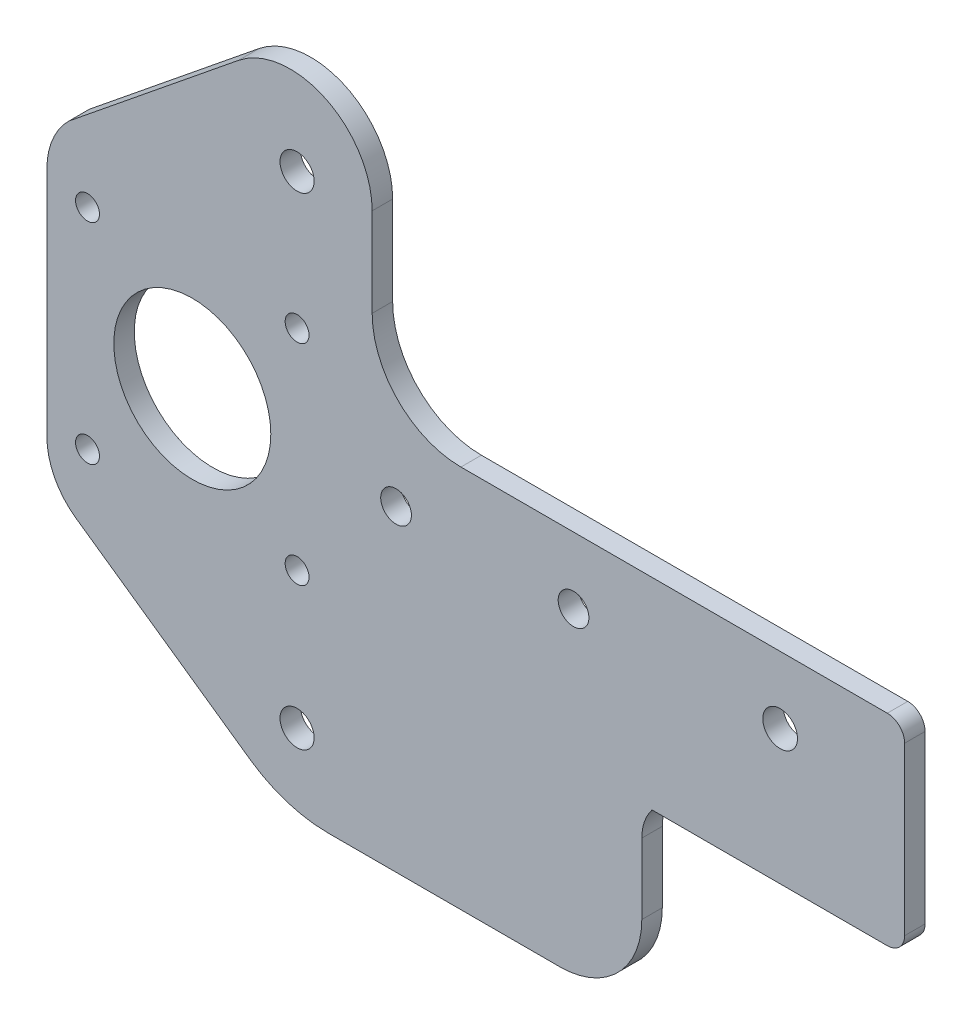
SolidWorks part; units mm, degrees
ref_plane "Front Plane" through (0, 0, 0) normal (0, 0, 1) x (1, 0, 0)
ref_plane "Top Plane" through (0, 0, 0) normal (0, 1, 0) x (1, 0, 0)
ref_plane "Right Plane" through (0, 0, 0) normal (1, 0, 0) x (0, 0, -1)
sketch "Sketch1" plane through (0, 0, 0) normal (0, 0, 1) x (1, 0, 0)
  line L0 (0, 0) -> (0, -29.5)
  line L1 (0, -29.5) -> (-37, -29.5)
  line L2 (0, 0) -> (-65, 0)
  line L3 (-78, 13) -> (-78, 26)
  line L4 (-97.5518, 35.3258) -> (-122.4205, 15.1875)
  line L5 (-125.65, 7.5017) -> (-125.65, -26.4983)
  line L6 (-89, 5.6) -> (-89, -25.1) construction
  line L7 (-119.7, 5.6) -> (-89, 5.6) construction
  line L8 (-121.3858, -34.6898) -> (-95.8858, -52.5451)
  line L9 (-84.4142, -56.1621) -> (-50.5, -56.1621)
  line L10 (-38.5, -44.1621) -> (-38.5, -33.8301)
  line L11 (-104.35, -9.75) -> (-104.35, 5.6) construction
  line L12 (-104.35, -9.75) -> (-89, -9.75) construction
  line L13 (-89, 25.5) -> (-89, -45.112) construction
  arc A0 (-78, 13) -> (-65, 0) centre (-65, 13) ccw
  arc A1 (-78, 26) -> (-97.5518, 35.3258) centre (-90, 26) ccw
  arc A2 (-122.4205, 15.1875) -> (-125.65, 7.5017) centre (-114.8895, 7.5017) ccw
  arc A3 (-125.65, -26.4983) -> (-121.3858, -34.6898) centre (-115.65, -26.4983) ccw
  arc A4 (-95.8858, -52.5451) -> (-84.4142, -56.1621) centre (-84.4142, -36.1621) ccw
  arc A5 (-50.5, -56.1621) -> (-38.5, -44.1621) centre (-50.5, -44.1621) ccw
  arc A6 (-37, -29.5) -> (-38.5, -33.8301) centre (-31.5, -33.8301) ccw
  circle A7 centre (-18.237, -9.806) radius 2.54
  circle A8 centre (-48.5, -9.75) radius 2.25
  circle A9 centre (-74.5, -9.75) radius 2.25
  circle A10 centre (-89, 5.6) radius 1.75
  circle A11 centre (-89, 25.5) radius 2.5
  circle A12 centre (-89, -25.1) radius 1.75
  circle A13 centre (-89, -45.112) radius 2.5
  circle A14 centre (-104.35, -9.75) radius 11.5
  circle A15 centre (-119.7, 5.6) radius 1.75
  circle A16 centre (-119.7, -25.1) radius 1.75
  dimension "D4" = 24
  dimension "D5" = 26
  dimension "D9" = 56.263
  dimension "D12" = 20
  dimension "D13" = 26
  dimension "D16" = 14
  dimension "D17" = 24
  dimension "D19" = 5.08
  dimension "D20" = 4.5
  dimension "D21" = 4.5
  dimension "D22" = 30.7
  dimension "D23" = 5
  dimension "D24" = 61.7621
  dimension "D25" = 5
  dimension "D26" = 30.7
  dimension "D27" = 23
  dimension "D11" = 3.5
  dimension "D1" = 65
  dimension "D2" = 29.5
  dimension "D3" = 37
  dimension "D6" = 13
  dimension "D7" = 32
  dimension "D8" = 51
  dimension "D10" = 34
  dimension "D14" = 125
  dimension "D15" = 25.5
  dimension "D18" = 1.5
  dimension "D29" = 70.763
  dimension "D30" = 9.75
  dimension "D31" = 9.75
  dimension "D34" = 25.5
  dimension "D37" = 70.612
  dimension "D39" = 35.306
  dimension "D42" = 89
extrude "Boss-Extrude1" add sketch "Sketch1" along normal blind 3
fillet "Fillet2" radius 2.54 2 edges at (0, 0, 1.5) (0, -29.5, 1.5)
